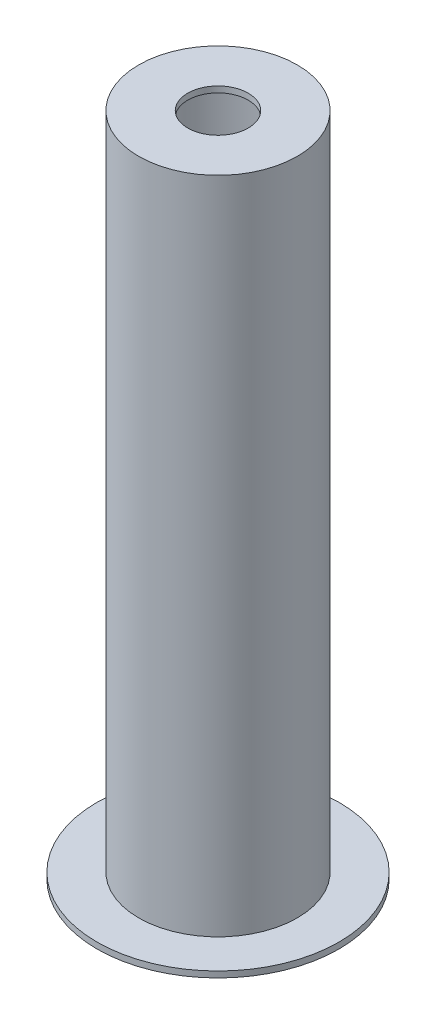
SolidWorks part; units mm, degrees
ref_plane "Plano frontal" through (0, 0, 0) normal (0, 0, 1) x (1, 0, 0)
ref_plane "Plano superior" through (0, 0, 0) normal (0, 1, 0) x (1, 0, 0)
ref_plane "Plano direito" through (0, 0, 0) normal (1, 0, 0) x (0, 0, -1)
sketch "Esboço1" plane through (0, 0, 0) normal (0, 0, 1) x (1, 0, 0)
  line L0 (0, 0) -> (0, 1100) construction
  line L1 (0, 0) -> (457.6466, 0) construction
  line L2 (50, 1100) -> (131, 1100)
  line L3 (131, 1100) -> (131, 10)
  line L4 (131, 10) -> (200, 10)
  line L5 (200, 10) -> (200, 0)
  line L6 (119, 0) -> (200, 0)
  line L7 (125, 10) -> (125, 1090)
  line L8 (125, 1090) -> (50, 1090)
  line L9 (125, 10) -> (119, 10)
  line L10 (50, 1100) -> (50, 1090)
  line L11 (119, 10) -> (119, 0)
  dimension "D1" = 250
  dimension "D2" = 6
  dimension "D3" = 10
  dimension "D4" = 10
  dimension "D5" = 1100
  dimension "D6" = 400
  dimension "D7" = 100
  dimension "D8" = 10
  dimension "D9" = 6
revolve "Revolução1" add sketch "Esboço1" angle 360 about L0
